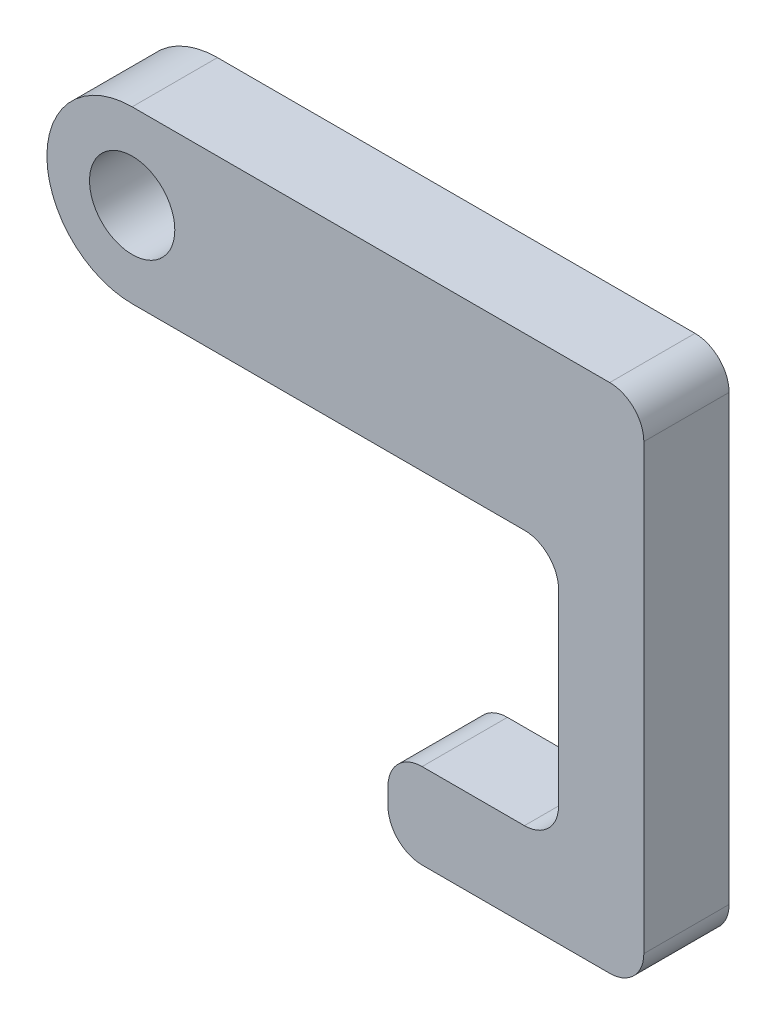
SolidWorks part; units mm, degrees
ref_plane "Plan de face" through (0, 0, 0) normal (0, 0, 1) x (1, 0, 0)
ref_plane "Plan de dessus" through (0, 0, 0) normal (0, 1, 0) x (1, 0, 0)
ref_plane "Plan de droite" through (0, 0, 0) normal (1, 0, 0) x (0, 0, -1)
sketch "Esquisse1" plane through (0, 0, 0) normal (0, 0, 1) x (1, 0, 0)
  line L0 (10, -5) -> (10, -20)
  line L1 (-15, 5) -> (15, 5)
  line L3 (-15, -5) -> (10, -5)
  line L4 (15, 5) -> (15, -5)
  line L5 (-15, 5) -> (15, -5) construction
  line L6 (-15, -5) -> (15, 5) construction
  line L7 (10, -20) -> (0, -20)
  line L8 (0, -20) -> (0, -25)
  line L9 (0, -25) -> (15, -25)
  line L10 (15, -25) -> (15, -5)
  line L11 (10, -20) -> (10, -25) construction
  line L12 (10, -5) -> (15, -5) construction
  arc A0 (-15, 5) -> (-15, -5) centre (-15, 0) ccw
  circle A1 centre (-15, 0) radius 2.5
  point P0 (0, 0)
  dimension "D2" = 30
  dimension "D3" = 5
  dimension "D1" = 10
  dimension "D4" = 5
  dimension "D5" = 5
  dimension "D6" = 20
  dimension "D7" = 10
extrude "Boss.-Extru.1" add sketch "Esquisse1" along normal blind 5
fillet "Congé1" radius 2 6 edges at (15, -25, 2.5) (15, 5, 2.5) (0, -25, 2.5) (0, -20, 2.5) (10, -20, 2.5) (10, -5, 2.5)
